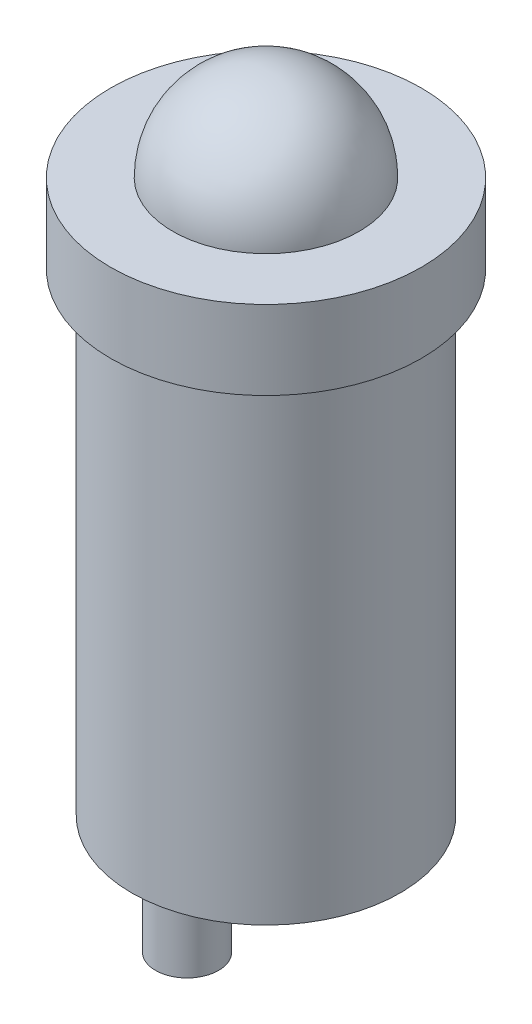
SolidWorks part; units mm, degrees
ref_plane "Front Plane" through (0, 0, 0) normal (0, 0, 1) x (1, 0, 0)
ref_plane "Top Plane" through (0, 0, 0) normal (0, 1, 0) x (1, 0, 0)
ref_plane "Right Plane" through (0, 0, 0) normal (1, 0, 0) x (0, 0, -1)
sketch "Sketch1" plane through (0, 0, 0) normal (0, 1, 0) x (1, 0, 0)
  circle A0 centre (0, 0) radius 2.16
  dimension "D1" = 4.32
extrude "Boss-Extrude1" add sketch "Sketch1" along normal blind 7.62
sketch "Sketch2" plane through (0, 7.62, 0) normal (0, 1, 0) x (1, 0, 0)
  circle A0 centre (0, 0) radius 2.5
  dimension "D1" = 5
extrude "Boss-Extrude2" add sketch "Sketch2" along normal blind 1.27
sketch "Sketch3" plane through (0, 8.89, 0) normal (0, 1, 0) x (1, 0, 0)
  line L0 (1.5, 0) -> (-1.5, 0)
  arc A0 (1.5, 0) -> (-1.5, 0) centre (0, 0) ccw
  point P5 (0, 0)
  dimension "D1" = 3
revolve "Revolve1" add sketch "Sketch3" angle 180 about L0
sketch "Sketch4" plane through (0, 0, 0) normal (0, -1, 0) x (1, 0, 0)
  line L0 (2.16, 0) -> (-2.16, 0) construction
  line L1 (0, -2.16) -> (0, 2.16) construction
  circle A0 centre (0, 0) radius 2.16 construction
  circle A1 centre (0, 1.27) radius 0.508
  circle A2 centre (0, -1.27) radius 0.508
  point P7 (0, 0)
  point P11 (0, 0)
  dimension "D1" = 1.016
  dimension "D2" = 1.27
extrude "Boss-Extrude3" add sketch "Sketch4" along normal blind 1.27 separate body
